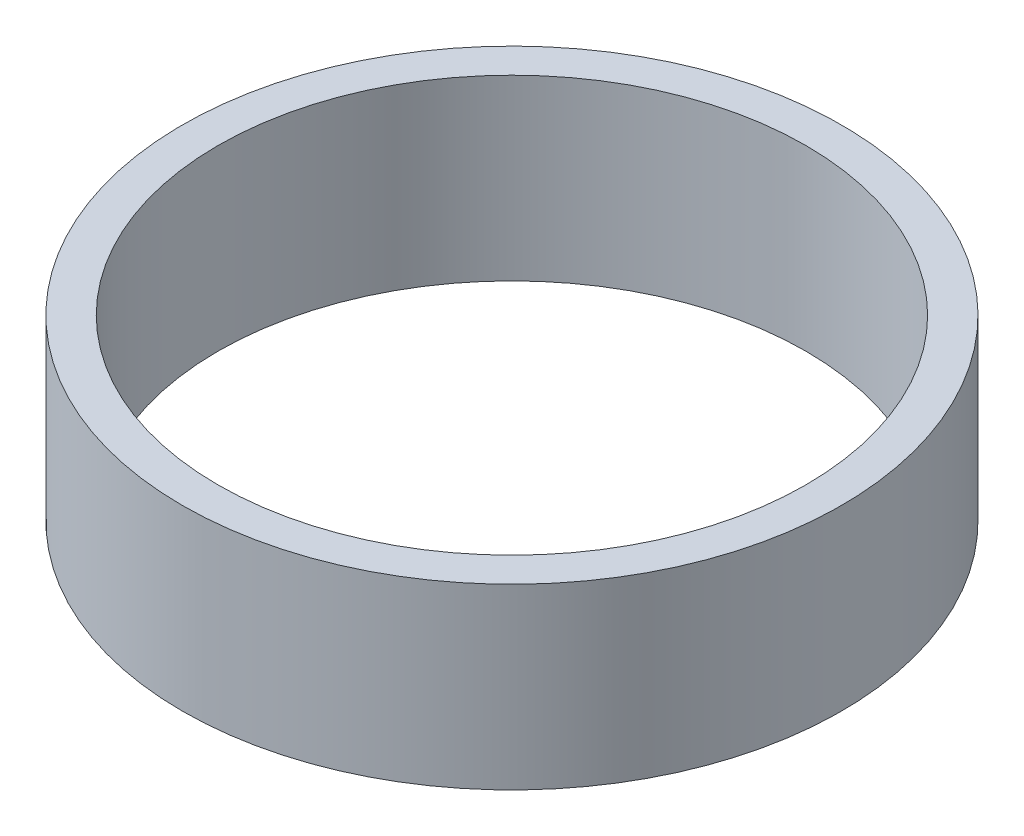
SolidWorks part; units mm, degrees
ref_plane "Front Plane" through (0, 0, 0) normal (0, 0, 1) x (1, 0, 0)
ref_plane "Top Plane" through (0, 0, 0) normal (0, 1, 0) x (1, 0, 0)
ref_plane "Right Plane" through (0, 0, 0) normal (1, 0, 0) x (0, 0, -1)
sketch "Sketch1" plane through (0, 0, 0) normal (0, 1, 0) x (1, 0, 0)
  circle A0 centre (0, 0) radius 16.5
  circle A1 centre (0, 0) radius 18.5
  dimension "D1" = 33
  dimension "D2" = 37
extrude "Boss-Extrude1" add sketch "Sketch1" along normal blind 10
